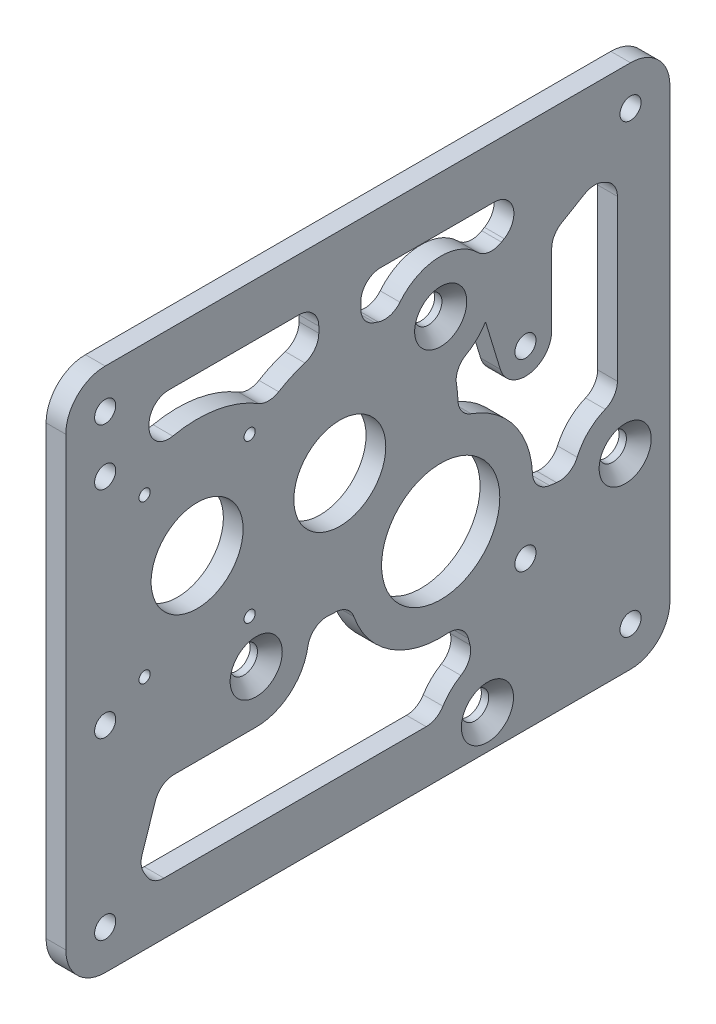
SolidWorks part; units mm, degrees
material "5052-H32"
ref_plane "Front Plane" through (0, 0, 0) normal (0, 0, 1) x (1, 0, 0)
ref_plane "Top Plane" through (0, 0, 0) normal (0, 1, 0) x (1, 0, 0)
ref_plane "Right Plane" through (0, 0, 0) normal (1, 0, 0) x (0, 0, -1)
sketch "Sketch1" plane through (0, 0, 0) normal (1, 0, 0) x (0, 0, -1)
  line L1 (0, 0) -> (146.05, 0)
  line L2 (0, 0) -> (0, 127)
  line L3 (0, 127) -> (146.05, 127)
  line L4 (146.05, 0) -> (146.05, 127)
  dimension "D1" = 146.05
  dimension "D2" = 127
extrude "Boss-Extrude2" add sketch "Sketch1" along normal blind 4.7625
sketch "Sketch2" plane through (4.7625, 0, 0) normal (1, 0, 0) x (0, 0, -1)
  line L0 (66.2432, 127) -> (66.2432, 0) construction
  line L1 (0, 127) -> (0, 0) construction
  line L2 (66.2432, 76.2) -> (90.6336, 51.8096) construction
  line L3 (0, 0) -> (146.05, 0) construction
  line L4 (146.05, 127) -> (0, 127) construction
  circle A0 centre (31.75, 76.2) radius 25.5016 construction
  circle A1 centre (90.6336, 51.8096) radius 8.9916 construction
  circle A2 centre (90.6336, 51.8096) radius 14.2875
  circle A3 centre (31.75, 76.2) radius 11.1125
  circle A4 centre (66.2432, 76.2) radius 25.5016 construction
  circle A5 centre (66.2432, 76.2) radius 8.9916 construction
  circle A6 centre (66.2432, 76.2) radius 11.1125
  dimension "D1" = 51.0032
  dimension "D2" = 17.9832
  dimension "D4" = 28.575
  dimension "D5" = 22.225
  dimension "D6" = 45
  dimension "D3" = 51.0032
  dimension "D7" = 17.9832
  dimension "D8" = 22.225
  dimension "D9" = 31.75
  dimension "D10" = 76.2
extrude "Cut-Extrude1" cut sketch "Sketch2" against normal through all
hole_wizard "CSK for M6 Flat Head Machine Screw1" positions "Sketch3" profile "Sketch4" countersink size "M6" standard "ANSI Metric" end condition through all
sketch "Sketch3" plane through (4.7625, 0, 0) normal (1, 0, 0) x (0, 0, -1)
  circle A1 centre (46.0336, 45.8096) radius 2.5 construction
  circle A2 centre (101.9336, 8.3096) radius 2.5 construction
  circle A3 centre (90.6336, 96.8096) radius 2.5 construction
  circle A4 centre (135.2336, 45.8096) radius 2.5 construction
  circle A5 centre (46.0336, 45.8096) radius 2.5
  circle A6 centre (101.9336, 8.3096) radius 2.5
  circle A7 centre (90.6336, 96.8096) radius 2.5
  circle A8 centre (135.2336, 45.8096) radius 2.5
  point P58 (101.9336, 8.3096)
  point P61 (46.0336, 45.8096)
  point P64 (135.2336, 45.8096)
  point P67 (90.6336, 96.8096)
sketch "Sketch4" plane through (4.7625, 96.8096, -90.6336) normal (0, 1, 0) x (0, 0, -1)
  line L0 (0, 0) -> (0, 4.7625)
  line L1 (0, 4.7625) -> (3.3, 4.7625)
  line L2 (3.3, 4.7625) -> (3.3, 3)
  line L3 (3.3, 3) -> (6.3, 0)
  line L5 (6.3, 0) -> (0, 0)
  line L6 (-3.3, 3) -> (-6.3, 0) construction
  line L11 (0, -6.35) -> (0, 107.95) construction
  dimension "Thru Hole Dia." = 6.6
  dimension "Thru Hole Depth" = 4.7625
  dimension "Near C'Sink Dia." = 12.6
  dimension "Near C'Sink Angle" = 90
hole_wizard "#10 Clearance Hole2" positions "Sketch5" profile "Sketch6" hole size "#10" standard "ANSI Inch" end condition through all
sketch "Sketch5" plane through (4.7625, 0, 0) normal (1, 0, 0) x (0, 0, -1)
  line L2 (9.525, 103.8796) -> (9.525, 51.8096)
  line L6 (0, 127) -> (0, 0) construction
  line L8 (111.125, 35.9346) -> (111.125, 80.3846)
  circle A2 centre (90.6336, 51.8096) radius 14.2875 construction
  point P423 (9.525, 103.8796)
  point P426 (111.125, 80.3846)
  point P432 (9.525, 51.8096)
  point P470 (111.125, 35.9346)
  dimension "D1" = 52.07
  dimension "D2" = 44.45
  dimension "D3" = 101.6
  dimension "D4" = 9.525
  dimension "D5" = 0
  dimension "D6" = 15.875
sketch "Sketch6" plane through (4.7625, 35.9346, -111.125) normal (0, 1, 0) x (0, 0, -1)
  line L0 (0, 0) -> (0, 4.7625)
  line L1 (0, 4.7625) -> (2.5527, 4.7625)
  line L2 (2.5527, 4.7625) -> (2.5527, 0)
  line L5 (2.5527, 0) -> (0, 0)
  line L11 (0, -6.35) -> (0, 107.95) construction
  dimension "Thru Hole Dia." = 5.1054
  dimension "Thru Hole Depth" = 4.7625
fillet "Fillet2" radius 9.525 4 edges at (2.3813, 127, 0) (2.3813, 0, 0) (2.3813, 0, -146.05) (2.3813, 127, -146.05)
hole_wizard "#10 Clearance Hole1" positions "Sketch7" profile "Sketch8" hole size "#10" standard "ANSI Inch" end condition through all
sketch "Sketch7" plane through (4.7625, 0, 0) normal (1, 0, 0) x (0, 0, -1)
  line L1 (9.525, 9.525) -> (136.525, 9.525)
  line L2 (9.525, 9.525) -> (9.525, 117.475)
  line L3 (9.525, 117.475) -> (136.525, 117.475)
  line L4 (136.525, 9.525) -> (136.525, 117.475)
  line L5 (136.525, 127) -> (9.525, 127) construction
  line L6 (0, 117.475) -> (0, 9.525) construction
  line L7 (146.05, 9.525) -> (146.05, 117.475) construction
  line L8 (9.525, 0) -> (136.525, 0) construction
  point P1 (9.525, 9.525)
  point P2 (136.525, 117.475)
  point P121 (9.525, 117.475)
  point P122 (136.525, 9.525)
  dimension "D1" = 9.525
  dimension "D2" = 9.525
  dimension "D3" = 9.525
  dimension "D4" = 9.525
sketch "Sketch8" plane through (4.7625, 9.525, -9.525) normal (0, 1, 0) x (0, 0, -1)
  line L0 (0, 0) -> (0, 4.7625)
  line L1 (0, 4.7625) -> (2.5527, 4.7625)
  line L2 (2.5527, 4.7625) -> (2.5527, 0)
  line L5 (2.5527, 0) -> (0, 0)
  line L11 (0, -6.35) -> (0, 107.95) construction
  dimension "Thru Hole Dia." = 5.1054
  dimension "Thru Hole Depth" = 4.7625
hole_wizard "#6-32 Tapped Hole1" positions "Sketch9" profile "Sketch10" tap size "#6-32" standard "ANSI Inch" end condition through all
sketch "Sketch9" plane through (0, 0, 0) normal (-1, 0, 0) x (0, 0, 1)
  line L2 (-44.45, 57.15) -> (-19.05, 57.15)
  line L3 (-44.45, 57.15) -> (-44.45, 95.25)
  line L4 (-44.45, 95.25) -> (-19.05, 95.25)
  line L5 (-19.05, 57.15) -> (-19.05, 95.25)
  line L6 (-44.45, 57.15) -> (-19.05, 95.25) construction
  line L7 (-44.45, 95.25) -> (-19.05, 57.15) construction
  point P17 (-31.75, 76.2)
  point P130 (-19.05, 57.15)
  point P133 (-44.45, 57.15)
  point P136 (-44.45, 95.25)
  point P139 (-19.05, 95.25)
  dimension "D1" = 38.1
  dimension "D2" = 25.4
sketch "Sketch10" plane through (0, 76.2, -31.75) normal (0, 1, 0) x (0, 0, 1)
  line L0 (0, 0) -> (0, 4.7625)
  line L1 (0, 4.7625) -> (1.3525, 4.7625)
  line L2 (1.3525, 4.7625) -> (1.3525, 0)
  line L5 (1.3525, 0) -> (0, 0)
  line L11 (0, -6.35) -> (0, 107.95) construction
  dimension "Thru Tap Drill Dia." = 2.7051
  dimension "Thru Tap Drill Depth" = 4.7625
cosmetic thread "Hole Thread1" parameters "D2"=3.5052
cosmetic thread "Hole Thread2" parameters "D2"=3.5052
cosmetic thread "Hole Thread3" parameters "D2"=3.5052
cosmetic thread "Hole Thread4" parameters "D2"=3.5052
sketch "Sketch11" plane through (4.7625, 0, 0) normal (1, 0, 0) x (0, 0, -1)
  line L0 (136.525, 9.525) -> (90.6336, 51.8096) construction
  line L1 (90.6336, 51.8096) -> (66.2432, 76.2) construction
  line L2 (66.2432, 76.2) -> (31.75, 76.2) construction
  line L3 (31.75, 76.2) -> (9.525, 117.475) construction
  line L4 (9.525, 117.475) -> (9.525, 9.525) construction
  line L5 (9.525, 9.525) -> (31.75, 76.2) construction
  line L6 (66.2432, 76.2) -> (136.525, 117.475) construction
  line L7 (9.525, 9.525) -> (136.525, 9.525) construction
  line L8 (9.525, 117.475) -> (136.525, 117.475) construction
  line L9 (0, 117.475) -> (0, 9.525) construction
  line L10 (146.05, 9.525) -> (146.05, 117.475) construction
  line L12 (20.1258, 114.3) -> (61.1632, 114.3)
  line L13 (121.0873, 114.3) -> (101.7099, 102.9201)
  line L14 (66.2432, 76.2) -> (66.2432, 117.475) construction
  line L15 (61.1632, 104.3198) -> (61.1632, 114.3)
  line L16 (71.3232, 104.3198) -> (71.3232, 114.3)
  line L17 (71.3232, 114.3) -> (121.0873, 114.3)
  line L18 (136.525, 117.475) -> (136.525, 9.525) construction
  line L19 (127.6319, 106.361) -> (117.475, 100.3961)
  line L20 (90.6336, 51.8096) -> (135.2336, 45.8096) construction
  line L21 (112.6601, 48.8464) -> (122.6965, 47.4962)
  line L22 (133.35, 103.5996) -> (133.35, 58.3186)
  line L23 (90.6336, 51.8096) -> (101.9336, 8.3096) construction
  line L24 (21.0149, 12.7) -> (90.0699, 12.7)
  line L25 (96.2215, 30.2986) -> (98.753, 20.5533)
  line L26 (22.758, 33.1596) -> (17.7545, 18.149)
  line L27 (46.0336, 33.1596) -> (22.758, 33.1596)
  line L28 (133.35, 103.5996) -> (127.6319, 106.361)
  line L29 (133.35, 103.5996) -> (136.525, 117.475) construction
  line L30 (136.525, 117.475) -> (127.6319, 106.361) construction
  line L31 (20.1258, 102.3038) -> (20.1258, 114.3)
  line L32 (117.475, 80.3846) -> (117.475, 100.3961)
  line L33 (105.0493, 78.5383) -> (101.4768, 90.2945)
  line L34 (21.0149, 12.7) -> (17.7545, 18.149)
  line L35 (17.7545, 18.149) -> (9.525, 9.525) construction
  line L36 (9.525, 9.525) -> (21.0149, 12.7) construction
  line L37 (93.5837, 84.5084) -> (92.1707, 89.158) construction
  circle A0 centre (9.525, 117.475) radius 9.525 construction
  circle A1 centre (31.75, 76.2) radius 28.575 construction
  arc A2 (61.1632, 104.3198) -> (71.3232, 104.3198) centre (66.2432, 76.2) ccw construction
  circle A3 centre (90.6336, 51.8096) radius 22.225 construction
  circle A4 centre (136.525, 9.525) radius 9.525 construction
  circle A5 centre (136.525, 117.475) radius 9.525 construction
  circle A6 centre (9.525, 9.525) radius 9.525 construction
  arc A7 (48.9966, 98.9834) -> (20.1258, 102.3038) centre (31.75, 76.2) ccw
  circle A8 centre (90.6336, 96.8096) radius 12.65 construction
  circle A9 centre (90.6336, 96.8096) radius 6.3 construction
  arc A11 (101.7099, 102.9201) -> (78.9971, 101.7709) centre (90.6336, 96.8096) ccw
  arc A12 (78.9971, 101.7709) -> (71.3232, 104.3198) centre (66.2432, 76.2) ccw
  arc A13 (61.1632, 104.3198) -> (48.9966, 98.9834) centre (66.2432, 76.2) ccw
  arc A15 (105.0493, 78.5383) -> (117.475, 80.3846) centre (111.125, 80.3846) ccw
  circle A16 centre (135.2336, 45.8096) radius 12.65 construction
  circle A17 centre (135.2336, 45.8096) radius 6.3 construction
  arc A20 (93.5837, 84.5084) -> (101.4768, 90.2945) centre (90.6336, 96.8096) ccw
  arc A21 (94.705, 73.6585) -> (93.5837, 84.5084) centre (66.2432, 76.2) ccw
  arc A22 (112.6601, 48.8464) -> (94.705, 73.6585) centre (90.6336, 51.8096) ccw
  arc A23 (133.35, 58.3186) -> (122.6965, 47.4962) centre (135.2336, 45.8096) ccw
  circle A24 centre (101.9336, 8.3096) radius 12.65 construction
  circle A25 centre (101.9336, 8.3096) radius 6.3 construction
  circle A26 centre (46.0336, 45.8096) radius 12.65 construction
  circle A27 centre (46.0336, 45.8096) radius 6.3 construction
  arc A28 (46.0336, 33.1596) -> (58.3395, 48.7398) centre (46.0336, 45.8096) ccw
  arc A29 (58.3395, 48.7398) -> (68.7847, 47.7382) centre (66.2432, 76.2) ccw
  arc A30 (68.7847, 47.7382) -> (96.2215, 30.2986) centre (90.6336, 51.8096) ccw
  arc A31 (98.753, 20.5533) -> (90.0699, 12.7) centre (101.9336, 8.3096) ccw
  dimension "D1" = 19.05
  dimension "D2" = 44.45
  dimension "D3" = 57.15
  dimension "D4" = 57.15
  dimension "D5" = 6.35
  dimension "D9" = 5.08
  dimension "D12" = 6.35
  dimension "D15" = 6.35
  dimension "D16" = 3.175
  dimension "D17" = 6.35
  dimension "D7" = 12.7
  dimension "D6" = 3.175
  dimension "D8" = 5.08
  dimension "D10" = 5.08
  dimension "D13" = 3.175
  dimension "D14" = 5.08
  dimension "D18" = 5.08
  dimension "D19" = 6.35
  dimension "D21" = 6.35
extrude "Cut-Extrude2" cut sketch "Sketch11" against normal through all
fillet "Fillet28" radius 4.7625 26 edges at (2.3813, 18.149, -17.7545) (2.3813, 12.7, -21.0149) (2.3813, 84.5084, -93.5837) (2.3813, 73.6585, -94.705) (2.3813, 48.8464, -112.6601) (2.3813, 47.4962, -122.6965) (2.3813, 58.3186, -133.35) (2.3813, 103.5996, -133.35) (2.3813, 106.361, -127.6319) (2.3813, 114.3, -121.0873) (2.3813, 102.9201, -101.7099) (2.3813, 114.3, -71.3232) (2.3813, 101.7709, -78.9971) (2.3813, 104.3198, -71.3232) (2.3813, 98.9834, -48.9966) (2.3813, 104.3198, -61.1632) (2.3813, 114.3, -61.1632) (2.3813, 114.3, -20.1258) (2.3813, 33.1596, -22.758) (2.3813, 48.7398, -58.3395) (2.3813, 47.7382, -68.7847) (2.3813, 30.2986, -96.2215) (2.3813, 20.5533, -98.753) (2.3813, 12.7, -90.0699) (2.3813, 102.3038, -20.1258) (2.3813, 100.3961, -117.475)
